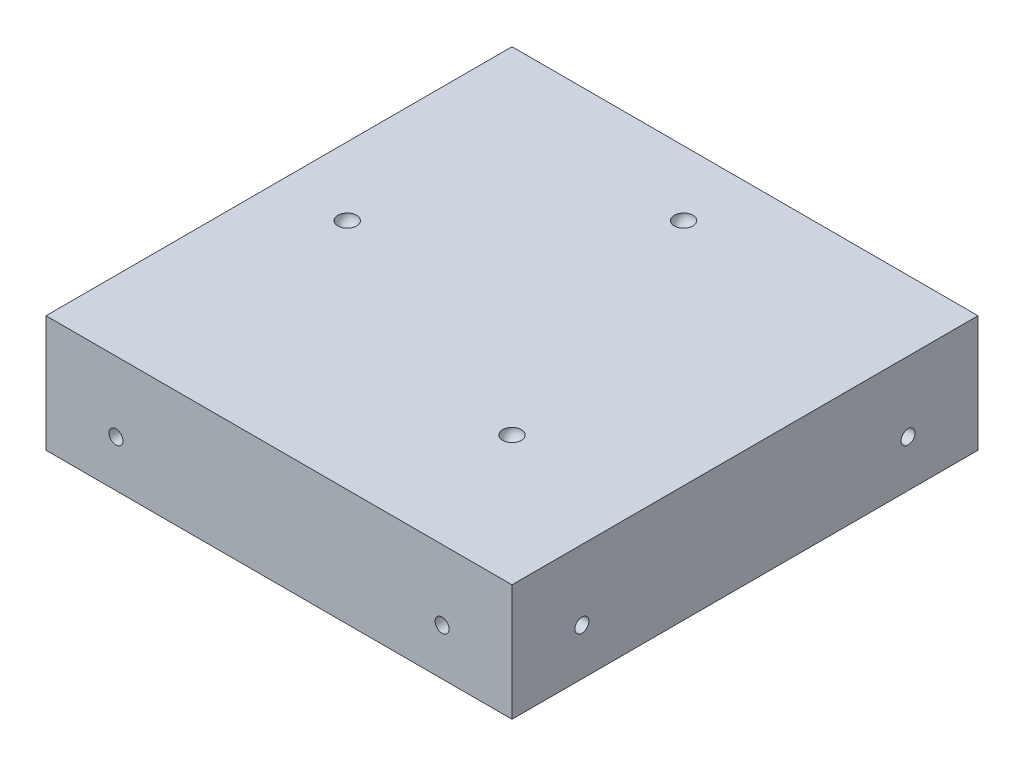
SolidWorks part; units mm, degrees
ref_plane "前视基准面" through (0, 0, 0) normal (0, 0, 1) x (1, 0, 0)
ref_plane "上视基准面" through (0, 0, 0) normal (0, 1, 0) x (1, 0, 0)
ref_plane "右视基准面" through (0, 0, 0) normal (1, 0, 0) x (0, 0, -1)
sketch "Sketch1" plane through (0, 0, 0) normal (0, 1, 0) x (1, 0, 0)
  line L1 (-50, 50) -> (50, 50)
  line L2 (-50, 50) -> (-50, -50)
  line L3 (-50, -50) -> (50, -50)
  line L4 (50, 50) -> (50, -50)
  line L5 (-50, 50) -> (50, -50) construction
  line L6 (-50, -50) -> (50, 50) construction
  point P0 (0, 0)
  dimension "D1" = 100
  dimension "D2" = 100
extrude "Boss-Extrude1" add sketch "Sketch1" along normal blind 25
sketch "Sketch2" plane through (0, 25, 0) normal (0, 1, 0) x (1, 0, 0)
  line L0 (-50, 50) -> (50, -50) construction
  line L1 (50, -50) -> (0, 0) construction
  line L2 (0, 0) -> (50, 50) construction
  line L3 (50, 50) -> (-50, -50) construction
  line L4 (-17.6777, 17.6777) -> (-50, -14.6447) construction
  line L5 (-50, 50) -> (-50, -50) construction
  line L6 (-50, -14.6447) -> (14.6447, 50) construction
  line L7 (50, 50) -> (-50, 50) construction
  line L8 (-36.7696, 1.4142) -> (-33.9411, -1.4142) construction
  line L9 (-36.7696, 1.4142) -> (-33.9411, -1.4142)
  line L12 (-1.4142, 36.7696) -> (2.4934, 32.8619) construction
  arc A0 (-36.7696, 1.4142) -> (-33.9411, -1.4142) centre (-35.3553, 0) cw
  dimension "D3" = 2
  dimension "D1" = 25
revolve "Cut-Revolve7" cut sketch "Sketch2" angle 360 about L8
sketch "Sketch3" plane through (0, 25, 0) normal (0, 1, 0) x (1, 0, 0)
  line L0 (-50, 50) -> (50, -50) construction
  line L1 (50, -50) -> (50, 50) construction
  line L2 (50, 50) -> (-50, 50) construction
  line L3 (50, -50) -> (50, 50) construction
  line L4 (50, 50) -> (-50, -50) construction
  line L5 (-50, 50) -> (-50, -50) construction
  line L6 (-50, -50) -> (50, -50) construction
  line L7 (-35.3553, 0) -> (14.6447, 50) construction
  line L8 (0.7337, 36.0891) -> (20.1077, 16.7151) construction
  line L9 (2.1479, 34.6749) -> (-8.0549, 44.8777) construction
  line L10 (2.1479, 34.6749) -> (-0.6805, 37.5033)
  arc A0 (2.1479, 34.6749) -> (-0.6805, 37.5033) centre (0.7337, 36.0891) ccw
  dimension "D3" = 2
  dimension "D1" = 90
  dimension "D2" = 27.399
revolve "Cut-Revolve8" cut sketch "Sketch3" angle 360 about L9
sketch "Sketch4" plane through (0, 25, 0) normal (0, 1, 0) x (1, 0, 0)
  line L0 (-50, 50) -> (50, -50) construction
  line L1 (-50, -50) -> (50, -50) construction
  line L2 (50, -50) -> (50, 50) construction
  line L3 (50, 50) -> (-50, -50) construction
  line L4 (0.7337, 36.0891) -> (-35.3553, 0) construction
  line L5 (-17.8322, 17.8322) -> (-17.8322, -50) construction
  line L6 (-17.8322, -50) -> (50, 17.8322) construction
  line L7 (50, 17.8322) -> (-17.8322, 17.8322) construction
  line L8 (23.582, -23.582) -> (20.7536, -20.7536)
  arc A0 (23.582, -23.582) -> (20.7536, -20.7536) centre (22.1678, -22.1678) ccw
  dimension "D1" = 2
  dimension "D2" = 40
revolve "Cut-Revolve9" cut sketch "Sketch4" angle 360 about L0
sketch "Sketch5" plane through (0, 0, 50) normal (0, 0, 1) x (1, 0, 0)
  line L0 (-50, 10) -> (50, 10) construction
  line L1 (-50, 25) -> (-50, 0) construction
  line L2 (50, 25) -> (50, 0) construction
  line L3 (50, 10) -> (50, 0) construction
  line L4 (-35, 25) -> (-35, 0) construction
  line L5 (-50, 25) -> (50, 25) construction
  line L6 (-50, 0) -> (50, 0) construction
  line L7 (35, 25) -> (35, 0) construction
  circle A0 centre (-35, 10) radius 1.5
  circle A1 centre (35, 10) radius 1.5
  dimension "D4" = 3
  dimension "D5" = 3
  dimension "D1" = 10
  dimension "D2" = 15
  dimension "D3" = 15
extrude "Cut-Extrude1" cut sketch "Sketch5" against normal blind 5
sketch "Sketch6" plane through (50, 0, 0) normal (1, 0, 0) x (0, 0, -1)
  line L0 (-50, 10) -> (50, 10) construction
  line L1 (-50, 25) -> (-50, 0) construction
  line L2 (50, 25) -> (50, 0) construction
  line L3 (-50, 0) -> (50, 0) construction
  line L4 (-35, 25) -> (-35, 0) construction
  line L5 (-50, 25) -> (50, 25) construction
  line L6 (35, 25) -> (35, 0) construction
  circle A0 centre (-35, 10) radius 1.5
  circle A1 centre (35, 10) radius 1.5
  dimension "D4" = 3
  dimension "D5" = 3
  dimension "D1" = 10
  dimension "D2" = 15
  dimension "D3" = 15
extrude "Cut-Extrude2" cut sketch "Sketch6" against normal blind 5
sketch "Sketch7" plane through (0, 0, -50) normal (0, 0, -1) x (-1, 0, 0)
  line L0 (-50, 10) -> (50, 10) construction
  line L1 (-50, 25) -> (-50, 0) construction
  line L2 (50, 25) -> (50, 0) construction
  line L3 (-50, 0) -> (50, 0) construction
  line L4 (-35, 25) -> (-35, -0.9288) construction
  line L5 (-50, 25) -> (50, 25) construction
  line L6 (35, 25) -> (35, 0) construction
  circle A0 centre (-35, 10) radius 1.5
  circle A1 centre (35, 10) radius 1.5
  dimension "D4" = 3
  dimension "D5" = 3
  dimension "D1" = 10
  dimension "D2" = 15
  dimension "D3" = 15
extrude "Cut-Extrude3" cut sketch "Sketch7" against normal blind 5
sketch "Sketch8" plane through (-50, 0, 0) normal (-1, 0, 0) x (0, 0, 1)
  line L0 (-50, 10) -> (50, 10) construction
  line L1 (-50, 25) -> (-50, 0) construction
  line L2 (50, 25) -> (50, 0) construction
  line L3 (-50, 0) -> (50, 0) construction
  line L4 (35, 25) -> (35, 0) construction
  line L5 (-35, 25) -> (-35, 0) construction
  line L6 (-50, 25) -> (50, 25) construction
  circle A0 centre (-35, 10) radius 1.5
  circle A1 centre (35, 10) radius 1.5
  dimension "D2" = 3
  dimension "D5" = 3
  dimension "D1" = 10
  dimension "D3" = 15
  dimension "D4" = 15
extrude "Cut-Extrude4" cut sketch "Sketch8" against normal blind 5
